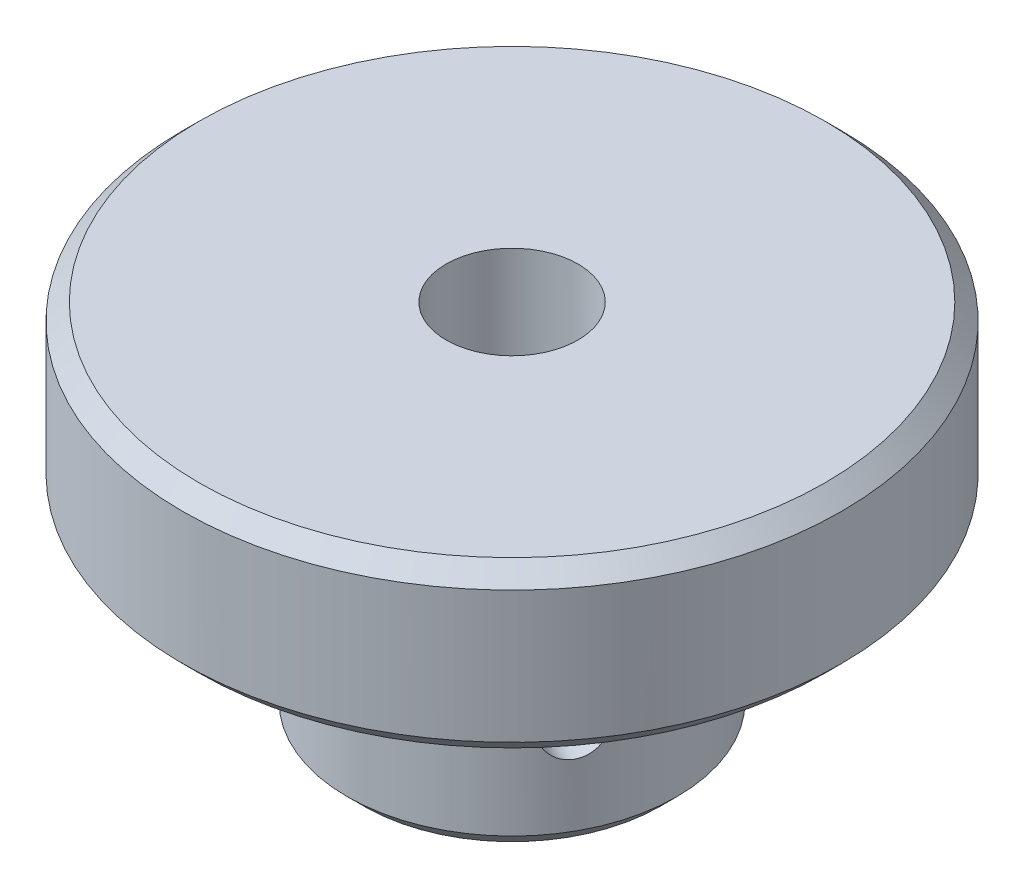
SolidWorks part; units mm, degrees
ref_plane "Front Plane" through (0, 0, 0) normal (0, 0, 1) x (1, 0, 0)
ref_plane "Top Plane" through (0, 0, 0) normal (0, 1, 0) x (1, 0, 0)
ref_plane "Right Plane" through (0, 0, 0) normal (1, 0, 0) x (0, 0, -1)
sketch "Sketch1" plane through (0, 0, 0) normal (0, 0, 1) x (1, 0, 0)
  line L0 (0, 10) -> (20, 10)
  line L1 (20, 10) -> (20, 0)
  line L2 (20, 0) -> (10, 0)
  line L3 (10, 0) -> (10, -12)
  line L4 (10, -12) -> (0, -12)
  line L5 (0, -12) -> (0, 10)
  dimension "D1" = 20
  dimension "D2" = 10
  dimension "D3" = 12
  dimension "D4" = 10
revolve "Revolve1" add sketch "Sketch1" angle 360 about L5
sketch "Sketch2" plane through (0, 10, 0) normal (0, 1, 0) x (1, 0, 0)
  circle A0 centre (0, 0) radius 4
  dimension "D1" = 8
extrude "Cut-Extrude1" cut sketch "Sketch2" against normal through all
chamfer "Chamfer1" distance 1 angle 45 3 edges at (10, -12, 0) (20, 10, 0) (20, 0, 0)
hole_wizard "M4x0.7 Tapped Hole1" positions "3DSketch1" profile "Sketch4" tap size "M4x0.7" standard "ANSI Metric"
sketch3d "3DSketch1"
  point P0 (-0.0853, -5.5638, -9.9996)
sketch "Sketch4" plane through (-0.0853, -5.5638, -9.9996) normal (0, 1, 0) x (-1, 0, 0.0085)
  line L0 (0, 0) -> (0, 20)
  line L1 (0, 20) -> (1.65, 20)
  line L2 (1.65, 20) -> (1.65, 0)
  line L5 (1.65, 0) -> (0, 0)
  line L11 (0, -6.35) -> (0, 107.95) construction
  dimension "Thru Tap Drill Dia." = 3.3
  dimension "Thru Tap Drill Depth" = 20
cosmetic thread "Hole Thread1" parameters "D2"=4
pattern_circular "CirPattern3" count 2 over 120 about axis through (0, -12, 0) along (0, -1, 0) of "M4x0.7 Tapped Hole1"
